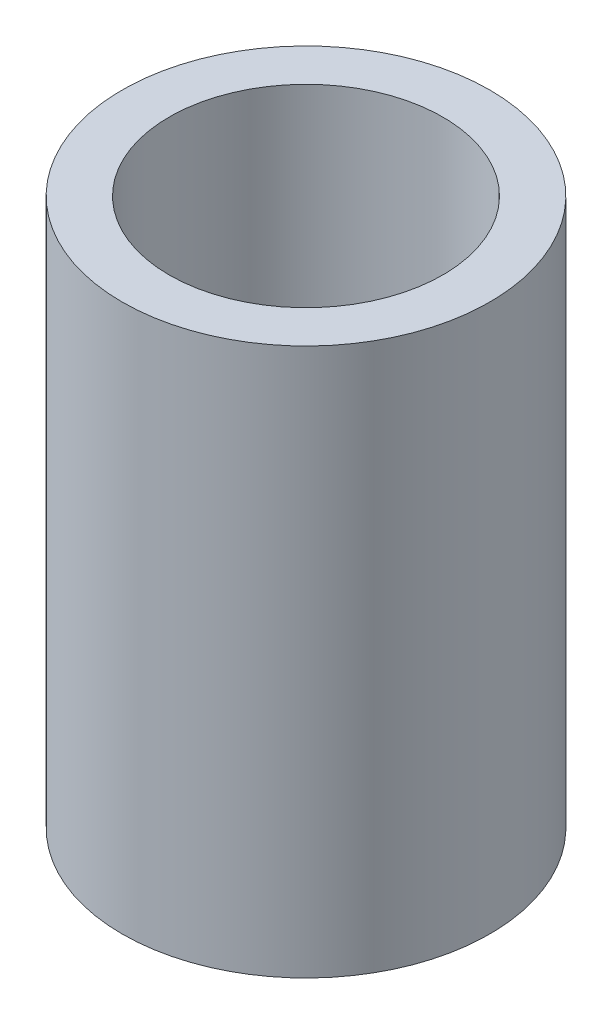
SolidWorks part; units mm, degrees
ref_plane "Front Plane" through (0, 0, 0) normal (0, 0, 1) x (1, 0, 0)
ref_plane "Top Plane" through (0, 0, 0) normal (0, 1, 0) x (1, 0, 0)
ref_plane "Right Plane" through (0, 0, 0) normal (1, 0, 0) x (0, 0, -1)
sketch "Sketch1" plane through (0, 0, 0) normal (0, 1, 0) x (1, 0, 0)
  circle A0 centre (0, 0) radius 4.7
  circle A1 centre (0, 0) radius 3.5
  dimension "D1" = 9.4
  dimension "D2" = 7
extrude "Boss-Extrude1" add sketch "Sketch1" along normal blind 14
